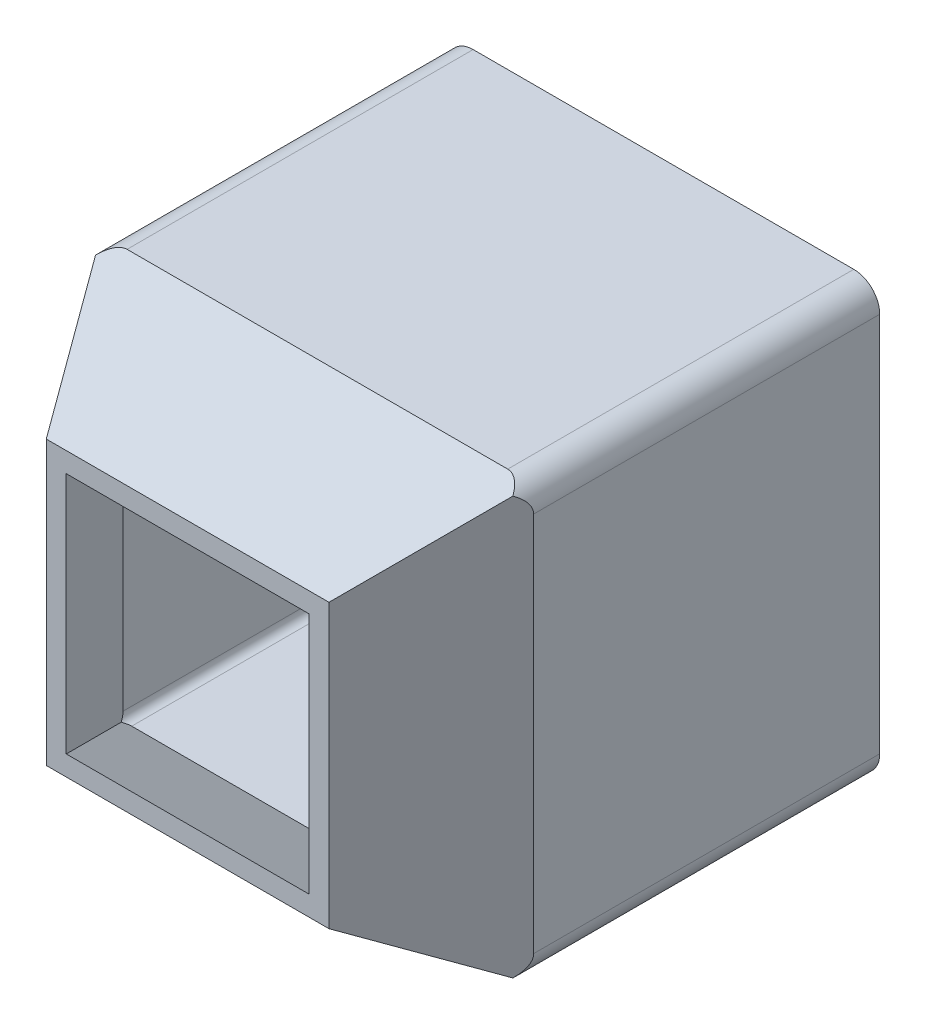
SolidWorks part; units mm, degrees
ref_plane "Front Plane" through (0, 0, 0) normal (0, 0, 1) x (1, 0, 0)
ref_plane "Top Plane" through (0, 0, 0) normal (0, 1, 0) x (1, 0, 0)
ref_plane "Right Plane" through (0, 0, 0) normal (1, 0, 0) x (0, 0, -1)
sketch "Sketch1" plane through (0, 0, 0) normal (0, 0, 1) x (1, 0, 0)
  line L1 (-20, 57.5) -> (30, 57.5)
  line L2 (-20, 57.5) -> (-20, 7.5)
  line L3 (-20, 7.5) -> (30, 7.5)
  line L4 (30, 57.5) -> (30, 7.5)
  line L5 (-20, 57.5) -> (30, 7.5) construction
  line L6 (-20, 7.5) -> (30, 57.5) construction
  line L7 (15, 7.5) -> (-5, 7.5) construction
  point P0 (5, 32.5)
  point P11 (5, 7.5)
  dimension "D1" = 50
extrude "Boss-Extrude1" add sketch "Sketch1" against normal blind 40
sketch "Sketch2" plane through (0, 0, 0) normal (0, 0, 1) x (1, 0, 0)
  line L4 (30, 7.5) -> (30, 57.5)
  line L5 (30, 57.5) -> (-20, 57.5)
  line L6 (-20, 57.5) -> (-20, 7.5)
  line L7 (-20, 7.5) -> (30, 7.5)
  line L8 (30, 7.5) -> (30, 57.5)
  line L9 (30, 57.5) -> (-20, 57.5)
  line L10 (-20, 57.5) -> (-20, 7.5)
  line L11 (-20, 7.5) -> (30, 7.5)
  dimension "D1" = 0
extrude "Boss-Extrude2" add sketch "Sketch2" along normal blind 15 draft 30
fillet "Fillet1" radius 3 4 edges at (-20, 7.5, -20) (30, 7.5, -20) (30, 57.5, -20) (-20, 57.5, -20)
shell "Shell1" thickness 2
